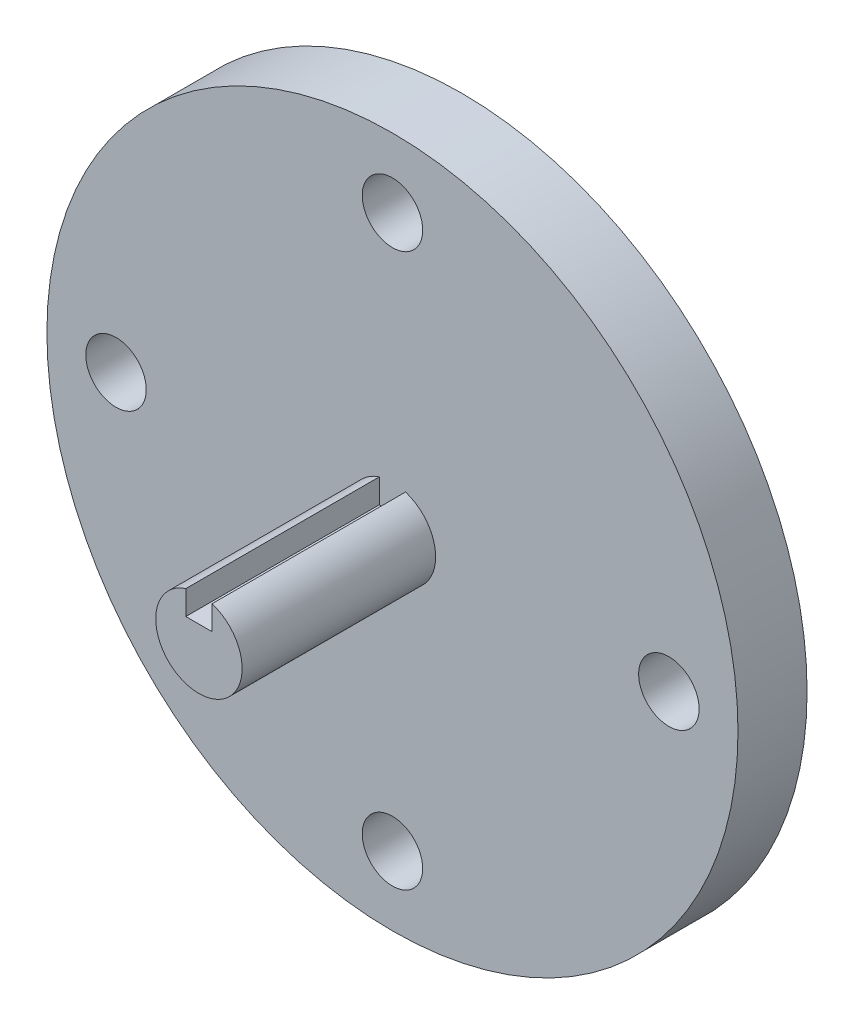
SolidWorks part; units mm, degrees
material "Cast Carbon Steel"
ref_plane "Front Plane" through (0, 0, 0) normal (0, 0, 1) x (1, 0, 0)
ref_plane "Top Plane" through (0, 0, 0) normal (0, 1, 0) x (1, 0, 0)
ref_plane "Right Plane" through (0, 0, 0) normal (1, 0, 0) x (0, 0, -1)
sketch "Sketch1" plane through (0, 0, 0) normal (0, 0, 1) x (1, 0, 0)
  circle A0 centre (0, 0) radius 63.5
  circle A2 centre (-50.8, 0) radius 5.5562
  circle A3 centre (0, 50.8) radius 5.5562
  circle A4 centre (50.8, 0) radius 5.5562
  circle A5 centre (0, -50.8) radius 5.5562
  point P15 (0, 0)
  dimension "D1" = 127
  dimension "D2" = 50.8
  dimension "D3" = 11.1125
  dimension "D4" = 4
extrude "Boss-Extrude1" add sketch "Sketch1" along normal blind 12.7
sketch "Sketch2" plane through (0, 0, 0) normal (0, 0, -1) x (-1, 0, 0)
  line L3 (-2.413, 7.5618) -> (-2.413, 3.1115)
  line L4 (-2.413, 3.1115) -> (2.413, 3.1115)
  line L5 (2.413, 3.1115) -> (2.413, 7.5618)
  arc A1 (-2.413, 7.5618) -> (2.413, 7.5618) centre (0, 0) ccw
  dimension "D2" = 15.875
  dimension "D3" = 4.4503
  dimension "D4" = 4.826
  dimension "D5" = 4.4503
extrude "Boss-Extrude5" add sketch "Sketch2" against normal blind 48.26
